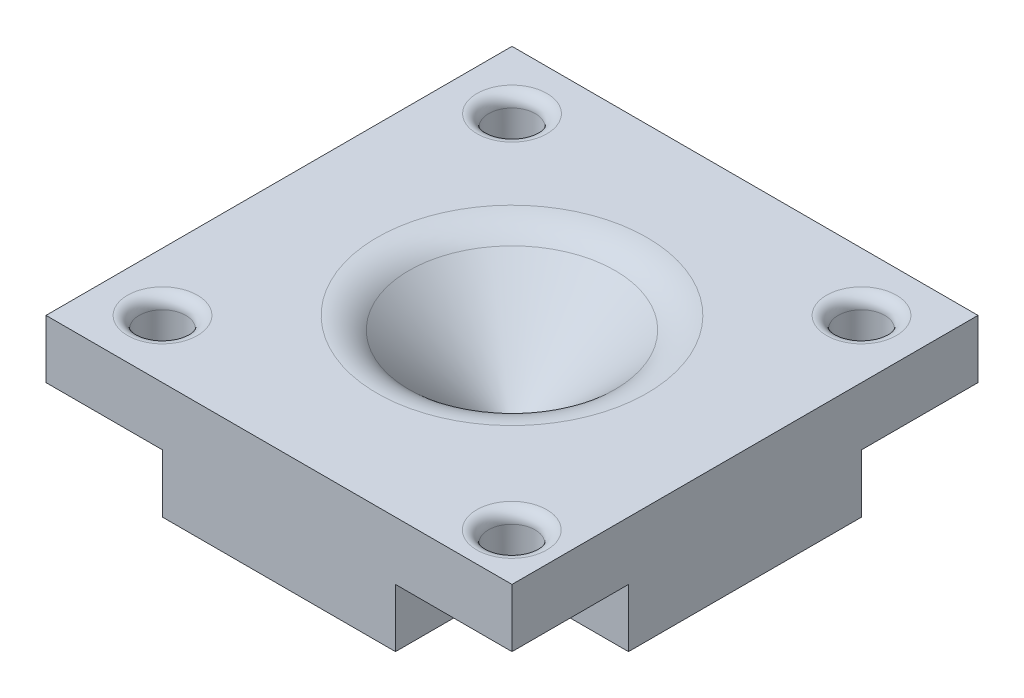
SolidWorks part; units mm, degrees
ref_plane "Front Plane" through (0, 0, 0) normal (0, 0, 1) x (1, 0, 0)
ref_plane "Top Plane" through (0, 0, 0) normal (0, 1, 0) x (1, 0, 0)
ref_plane "Right Plane" through (0, 0, 0) normal (1, 0, 0) x (0, 0, -1)
sketch "Sketch1" plane through (0, 0, 0) normal (0, 1, 0) x (1, 0, 0)
  line L1 (0, 0) -> (20, 0)
  line L2 (0, 0) -> (0, 20)
  line L3 (0, 20) -> (20, 20)
  line L4 (20, 0) -> (20, 20)
  dimension "D1" = 20
  dimension "D2" = 20
extrude "Boss-Extrude1" add sketch "Sketch1" along normal blind 5
ref_plane "Plane1" through (10, 0, 0) normal (1, 0, 0) x (0, 0, -1)
sketch "Sketch3" plane through (10, 0, 0) normal (1, 0, 0) x (0, 0, -1)
  line L0 (10, 5) -> (10, 0)
  line L1 (0, 5) -> (20, 5) construction
  line L2 (0, 0) -> (20, 0) construction
  line L3 (5, 5) -> (10, 0.3)
  line L4 (5, 5) -> (10, 5)
  dimension "D1" = 5
  dimension "D2" = 0.3
revolve "Cut-Revolve3" cut sketch "Sketch3" angle 360 about L0
sketch "Sketch4" plane through (0, 5, 0) normal (0, 1, 0) x (1, 0, 0)
  line L0 (0, 20) -> (0, 0) construction
  line L1 (9.75, 10.25) -> (10.25, 10.25)
  line L2 (9.75, 10.25) -> (9.75, 9.75)
  line L3 (9.75, 9.75) -> (10.25, 9.75)
  line L4 (10.25, 10.25) -> (10.25, 9.75)
  line L5 (20, 0) -> (20, 20) construction
  line L6 (20, 20) -> (0, 20) construction
  line L7 (0, 0) -> (20, 0) construction
  point P6 (0, 10)
  dimension "D1" = 9.75
  dimension "D2" = 9.75
  dimension "D3" = 9.75
  dimension "D4" = 9.75
extrude "Cut-Extrude1" cut sketch "Sketch4" against normal blind 7
fillet "Fillet1" radius 2 1 edges at (10, 5, -5)
sketch "Sketch5" plane through (0, 0, 0) normal (0, -1, 0) x (-1, 0, 0)
  line L1 (-20, 20) -> (-15, 20)
  line L2 (-20, 20) -> (-20, 15)
  line L3 (-20, 15) -> (-15, 15)
  line L4 (-15, 20) -> (-15, 15)
  line L5 (0, 20) -> (-5, 20)
  line L6 (0, 20) -> (0, 15)
  line L7 (0, 15) -> (-5, 15)
  line L8 (-5, 20) -> (-5, 15)
  line L9 (-20, 0) -> (-15, 0)
  line L10 (-20, 0) -> (-20, 5)
  line L11 (-20, 5) -> (-15, 5)
  line L12 (-15, 0) -> (-15, 5)
  line L13 (0, 0) -> (-5, 0)
  line L14 (0, 0) -> (0, 5)
  line L15 (0, 5) -> (-5, 5)
  line L16 (-5, 0) -> (-5, 5)
  dimension "D1" = 5
  dimension "D2" = 5
  dimension "D3" = 5
  dimension "D4" = 5
  dimension "D5" = 5
  dimension "D6" = 5
  dimension "D7" = 5
  dimension "D8" = 5
extrude "Cut-Extrude2" cut sketch "Sketch5" against normal blind 2.5
sketch "Sketch6" plane through (0, 5, 0) normal (0, 1, 0) x (1, 0, 0)
  line L0 (20, 20) -> (0, 20) construction
  line L1 (20, 0) -> (20, 20) construction
  line L2 (0, 20) -> (0, 0) construction
  line L3 (0, 0) -> (20, 0) construction
  circle A0 centre (17.9666, 2.0238) radius 1
  circle A1 centre (17.5, 17.5) radius 1
  circle A2 centre (2.5, 17.5) radius 1
  circle A3 centre (2.5, 2.5) radius 1
  dimension "D1" = 2.5
  dimension "D2" = 2.5
  dimension "D3" = 2.5
  dimension "D4" = 2.5
  dimension "D5" = 2.5
  dimension "D6" = 2.5
  dimension "D7" = 2
  dimension "D8" = 2
  dimension "D9" = 2
  dimension "D10" = 2
extrude "Cut-Extrude3" cut sketch "Sketch6" against normal blind 3
fillet "Fillet2" radius 0.5 4 edges at (2.5, 5, -1.5) (17.9666, 5, -1.0238) (17.5, 5, -16.5) (2.5, 5, -16.5)
